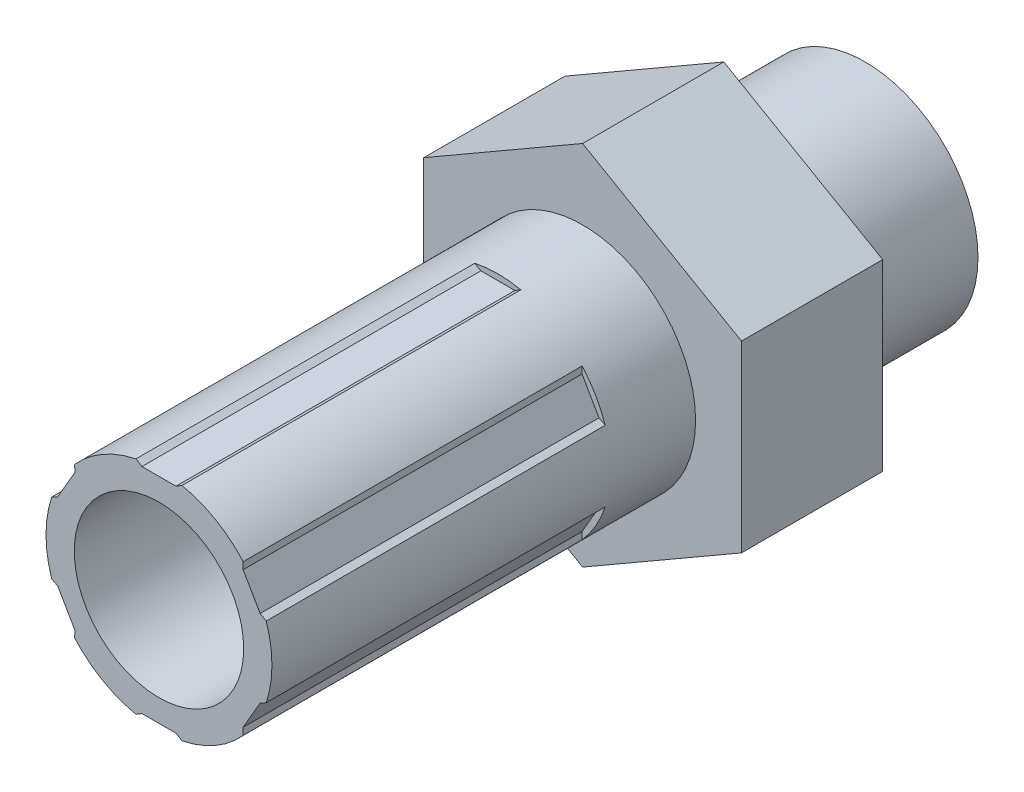
SolidWorks part; units mm, degrees
material "Alloy Steel"
ref_plane "Front Plane" through (0, 0, 0) normal (0, 0, 1) x (1, 0, 0)
ref_plane "Top Plane" through (0, 0, 0) normal (0, 1, 0) x (1, 0, 0)
ref_plane "Right Plane" through (0, 0, 0) normal (1, 0, 0) x (0, 0, -1)
sketch "Sketch1" plane through (0, 0, 0) normal (0, 0, 1) x (1, 0, 0)
  line L1 (0, 8.2489) -> (-7.1438, 4.1244)
  line L2 (-7.1438, 4.1244) -> (-7.1438, -4.1244)
  line L3 (-7.1438, -4.1244) -> (0, -8.2489)
  line L4 (0, -8.2489) -> (7.1437, -4.1244)
  line L5 (7.1437, -4.1244) -> (7.1437, 4.1244)
  line L6 (7.1437, 4.1244) -> (0, 8.2489)
  circle A0 centre (0, 0) radius 7.1437 construction
  dimension "D1" = 14.2875
extrude "Boss-Extrude1" add sketch "Sketch1" along normal blind 6.35
sketch "Sketch2" plane through (0, 0, 0) normal (0, 0, -1) x (-1, 0, 0)
  circle A0 centre (0, 0) radius 5.08
  dimension "D1" = 10.16
extrude "Boss-Extrude2" add sketch "Sketch2" along normal blind 6.35
sketch "Sketch3" plane through (0, 0, 6.35) normal (0, 0, 1) x (1, 0, 0)
  circle A0 centre (0, 0) radius 5.08
  dimension "D1" = 10.16
extrude "Boss-Extrude3" add sketch "Sketch3" along normal blind 19.05
sketch "Sketch4" plane through (0, 0, 25.4) normal (0, 0, 1) x (1, 0, 0)
  circle A0 centre (0, 0) radius 3.81
  dimension "D1" = 7.62
extrude "Cut-Extrude1" cut sketch "Sketch4" against normal through all
sketch "Sketch5" plane through (0, 0, 25.4) normal (0, 0, 1) x (1, 0, 0)
  line L0 (0, 4.8109) -> (0.765, 4.8109)
  line L1 (0.765, 4.8109) -> (1.27, 5.1149)
  line L2 (1.27, 5.1149) -> (0, 5.1149)
  line L3 (0, 5.1149) -> (0, 4.8109) construction
  line L4 (0, 4.8109) -> (-0.765, 4.8109)
  line L5 (-0.765, 4.8109) -> (-1.27, 5.1149)
  line L6 (-1.27, 5.1149) -> (0, 5.1149)
  dimension "D1" = 2.54
extrude "Cut-Extrude2" cut sketch "Sketch5" against normal blind 15.24
pattern_circular "CirPattern1" count 6 over 360 about axis through (0, 0, 0) along (0, 0, 1) of "Cut-Extrude2"
